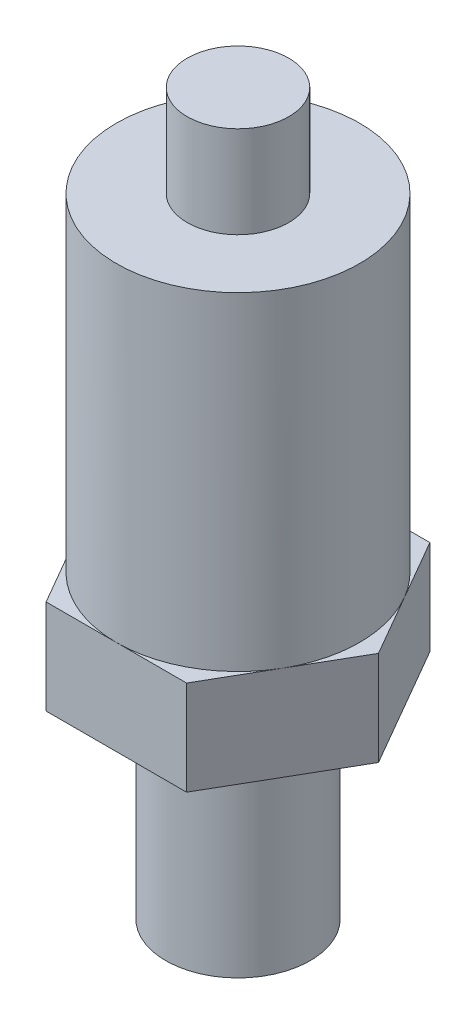
SolidWorks part; units mm, degrees
material "Cast Stainless Steel"
ref_plane "Front Plane" through (0, 0, 0) normal (0, 0, 1) x (1, 0, 0)
ref_plane "Top Plane" through (0, 0, 0) normal (0, 1, 0) x (1, 0, 0)
ref_plane "Right Plane" through (0, 0, 0) normal (1, 0, 0) x (0, 0, -1)
sketch "Sketch1" plane through (0, 0, 0) normal (0, 0, 1) x (1, 0, 0)
  line L0 (0, 0) -> (0, 29.972)
  line L1 (0, 29.972) -> (6.477, 29.972)
  line L2 (6.477, 29.972) -> (6.477, 38.354)
  line L3 (6.477, 38.354) -> (11.1125, 38.354)
  line L4 (11.1125, 38.354) -> (11.1125, 0)
  line L5 (11.1125, 0) -> (11.1125, -27.432)
  line L6 (0, 0) -> (0, -8.636)
  line L7 (0, -8.636) -> (4.5125, -8.636)
  line L8 (4.5125, -8.636) -> (4.5125, -27.432)
  line L9 (4.5125, -27.432) -> (11.1125, -27.432)
  point P8 (0, 0)
  point P11 (14.1423, -18.401)
  dimension "D1" = 29.972
  dimension "D2" = 8.382
  dimension "D3" = 11.1125
  dimension "D4" = 4.6355
  dimension "D5" = 6.6
  dimension "D6" = 8.636
  dimension "D7" = 27.432
revolve "Revolve1" add sketch "Sketch1" angle 360 about L4
sketch "Sketch2" plane through (0, -8.636, 0) normal (0, -1, 0) x (1, 0, 0)
  line L1 (23.9441, 0) -> (17.5283, 11.1125)
  line L2 (17.5283, 11.1125) -> (4.6967, 11.1125)
  line L3 (4.6967, 11.1125) -> (-1.7191, 0)
  line L4 (-1.7191, 0) -> (4.6967, -11.1125)
  line L5 (4.6967, -11.1125) -> (17.5283, -11.1125)
  line L6 (17.5283, -11.1125) -> (23.9441, 0)
  circle A0 centre (11.1125, 0) radius 6.6 construction
  circle A1 centre (11.1125, 0) radius 6.6 construction
  circle A2 centre (11.1125, 0) radius 11.1125 construction
  dimension "D1" = 22.225
extrude "Boss-Extrude1" add sketch "Sketch2" against normal blind 8.636
